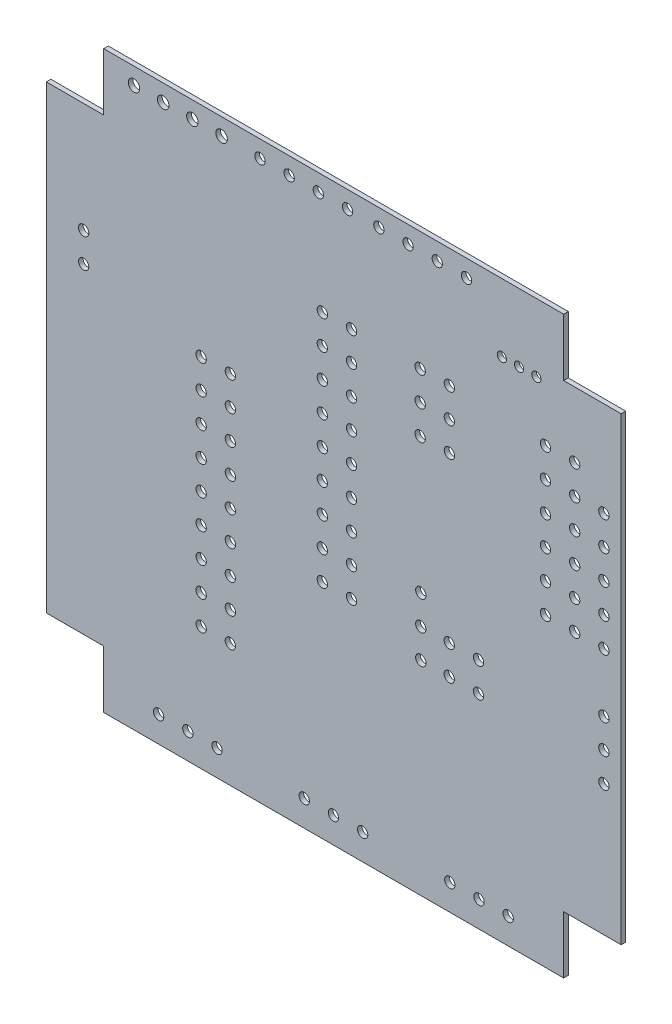
SolidWorks part; units mm, degrees
ref_plane "Спереди" through (0, 0, 0) normal (0, 0, 1) x (1, 0, 0)
ref_plane "Сверху" through (0, 0, 0) normal (0, 1, 0) x (1, 0, 0)
ref_plane "Справа" through (0, 0, 0) normal (1, 0, 0) x (0, 0, -1)
ref_plane "Плоскость1" through (0, 0, 0) normal (0, 0, -1) x (-1, 0, 0)
sketch "Эскиз1" plane through (0, 0, 0) normal (0, 0, -1) x (-1, 0, 0)
  line L0 (-49.9892, 4.9742) -> (-44.9892, 4.9742)
  line L1 (-44.9892, 4.9742) -> (-44.9892, -0.0258)
  line L2 (-44.9892, -0.0258) -> (-4.9892, -0.0258)
  line L3 (-4.9892, -0.0258) -> (-4.9892, 4.9742)
  line L4 (-4.9892, 4.9742) -> (0.0108, 4.9742)
  line L5 (0.0108, 4.9742) -> (0.0108, 44.9742)
  line L6 (0.0108, 44.9742) -> (-4.9892, 44.9742)
  line L7 (-4.9892, 44.9742) -> (-4.9892, 49.9742)
  line L8 (-4.9892, 49.9742) -> (-44.9892, 49.9742)
  line L9 (-44.9892, 49.9742) -> (-44.9892, 44.9742)
  line L10 (-44.9892, 44.9742) -> (-49.9892, 44.9742)
  line L11 (-49.9892, 44.9742) -> (-49.9892, 4.9742)
  circle A0 centre (-48.4893, 36.7242) radius 0.45
  circle A1 centre (-45.9493, 39.2742) radius 0.45
  circle A2 centre (-45.9493, 36.7242) radius 0.45
  circle A3 centre (-42.6142, 44.0742) radius 0.4
  circle A4 centre (-41.1142, 44.0742) radius 0.4
  circle A5 centre (-43.4093, 39.2742) radius 0.45
  circle A6 centre (-48.4893, 34.1742) radius 0.45
  circle A7 centre (-45.9493, 34.1742) radius 0.45
  circle A8 centre (-48.4893, 31.6242) radius 0.45
  circle A9 centre (-43.4093, 34.1742) radius 0.45
  circle A10 centre (-43.4093, 36.7242) radius 0.45
  circle A11 centre (-45.9493, 31.6242) radius 0.45
  circle A12 centre (-39.6142, 44.0742) radius 0.4
  circle A13 centre (-36.5392, 48.4742) radius 0.45
  circle A14 centre (-35.052, 39.624) radius 0.45
  circle A15 centre (-31.4592, 48.4742) radius 0.45
  circle A16 centre (-28.9192, 48.4742) radius 0.45
  circle A17 centre (-33.9992, 48.4742) radius 0.45
  circle A18 centre (-35.052, 37.084) radius 0.45
  circle A19 centre (-32.512, 39.624) radius 0.45
  circle A20 centre (-35.052, 34.544) radius 0.45
  circle A21 centre (-32.512, 34.544) radius 0.45
  circle A22 centre (-32.512, 37.084) radius 0.45
  circle A23 centre (-26.543, 34.544) radius 0.45
  circle A24 centre (-48.4893, 29.0742) radius 0.45
  circle A25 centre (-45.9493, 29.0742) radius 0.45
  circle A26 centre (-48.4893, 26.5242) radius 0.45
  circle A27 centre (-43.4093, 29.0742) radius 0.45
  circle A28 centre (-43.4093, 31.6242) radius 0.45
  circle A29 centre (-45.9493, 26.5242) radius 0.45
  circle A30 centre (-48.4893, 18.8842) radius 0.45
  circle A31 centre (-48.4893, 21.4242) radius 0.45
  circle A32 centre (-48.4893, 16.3442) radius 0.45
  circle A33 centre (-43.4093, 26.5242) radius 0.45
  circle A34 centre (-40.1693, 2.2242) radius 0.45
  circle A35 centre (-37.6293, 2.2242) radius 0.45
  circle A36 centre (-35.0394, 20.2341) radius 0.45
  circle A37 centre (-32.5643, 22.7741) radius 0.45
  circle A38 centre (-37.5894, 20.2341) radius 0.45
  circle A39 centre (-26.543, 24.384) radius 0.45
  circle A40 centre (-26.543, 29.464) radius 0.45
  circle A41 centre (-26.543, 21.844) radius 0.45
  circle A42 centre (-37.5894, 17.6941) radius 0.45
  circle A43 centre (-35.0394, 17.6941) radius 0.45
  circle A44 centre (-35.0893, 2.2242) radius 0.45
  circle A45 centre (-32.5643, 17.6941) radius 0.45
  circle A46 centre (-32.5643, 20.2341) radius 0.45
  circle A47 centre (-27.5068, 2.2242) radius 0.45
  circle A48 centre (-26.543, 39.624) radius 0.45
  circle A49 centre (-26.1942, 48.4892) radius 0.45
  circle A50 centre (-26.543, 37.084) radius 0.45
  circle A51 centre (-24.003, 39.624) radius 0.45
  circle A52 centre (-23.6542, 48.4892) radius 0.45
  circle A53 centre (-24.003, 37.084) radius 0.45
  circle A54 centre (-26.543, 32.004) radius 0.45
  circle A55 centre (-24.003, 32.004) radius 0.45
  circle A56 centre (-26.543, 26.924) radius 0.45
  circle A57 centre (-24.003, 29.464) radius 0.45
  circle A58 centre (-24.003, 34.544) radius 0.45
  circle A59 centre (-24.003, 26.924) radius 0.45
  circle A60 centre (-21.1142, 48.4892) radius 0.45
  circle A61 centre (-18.5742, 48.4892) radius 0.45
  circle A62 centre (-15.24, 48.514) radius 0.5
  circle A63 centre (-10.16, 48.514) radius 0.5
  circle A64 centre (-7.62, 48.514) radius 0.5
  circle A65 centre (-12.7, 48.514) radius 0.5
  circle A66 centre (-16.002, 28.464) radius 0.45
  circle A67 centre (-16.002, 31.004) radius 0.45
  circle A68 centre (-13.462, 28.464) radius 0.45
  circle A69 centre (-3.2393, 32.8742) radius 0.45
  circle A70 centre (-3.2393, 35.4142) radius 0.45
  circle A71 centre (-13.462, 31.004) radius 0.45
  circle A72 centre (-24.003, 21.844) radius 0.45
  circle A73 centre (-24.003, 24.384) radius 0.45
  circle A74 centre (-26.543, 19.304) radius 0.45
  circle A75 centre (-16.002, 23.384) radius 0.45
  circle A76 centre (-16.002, 25.924) radius 0.45
  circle A77 centre (-16.002, 20.844) radius 0.45
  circle A78 centre (-24.9668, 2.2242) radius 0.45
  circle A79 centre (-24.003, 19.304) radius 0.45
  circle A80 centre (-22.4268, 2.2242) radius 0.45
  circle A81 centre (-16.002, 15.764) radius 0.45
  circle A82 centre (-16.002, 18.304) radius 0.45
  circle A83 centre (-16.002, 13.224) radius 0.45
  circle A84 centre (-13.462, 15.764) radius 0.45
  circle A85 centre (-13.462, 18.304) radius 0.45
  circle A86 centre (-13.462, 13.224) radius 0.45
  circle A87 centre (-13.462, 23.384) radius 0.45
  circle A88 centre (-13.462, 25.924) radius 0.45
  circle A89 centre (-13.462, 20.844) radius 0.45
  circle A90 centre (-16.002, 10.684) radius 0.45
  circle A91 centre (-13.462, 10.684) radius 0.45
  circle A92 centre (-14.8443, 2.2242) radius 0.45
  circle A93 centre (-9.7643, 2.2242) radius 0.45
  circle A94 centre (-12.3043, 2.2242) radius 0.45
extrude "Бобышка-Вытянуть1" add sketch "Эскиз1" against normal blind 0.4013
